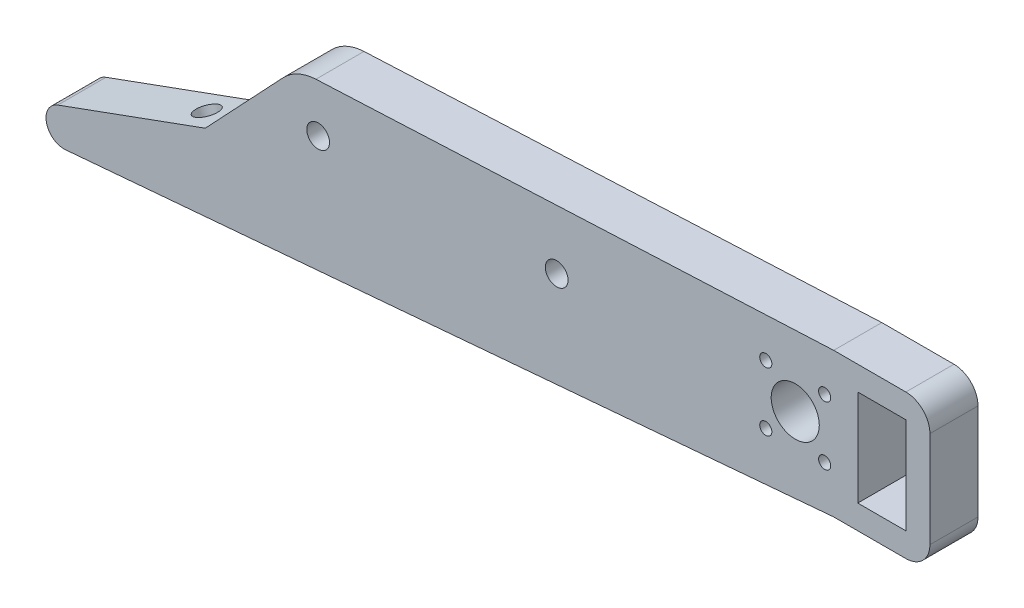
SolidWorks part; units mm, degrees
material "PE High Density"
ref_plane "Front Plane" through (0, 0, 0) normal (0, 0, 1) x (1, 0, 0)
ref_plane "Top Plane" through (0, 0, 0) normal (0, 1, 0) x (1, 0, 0)
ref_plane "Right Plane" through (0, 0, 0) normal (1, 0, 0) x (0, 0, -1)
sketch "Sketch1" plane through (0, 0, 0) normal (0, 0, 1) x (1, 0, 0)
  line L0 (27.6069, 3.8891) -> (35.3851, -3.8891) construction
  line L1 (0, -55) -> (0, 55) construction
  line L2 (27.6069, -3.8891) -> (35.3851, 3.8891) construction
  line L3 (-1001.9207, 0) -> (48998.0793, 0) construction
  line L4 (-969.6313, -19.05) -> (49030.3687, -19.05) construction
  line L5 (36.576, 9.525) -> (49.276, 9.525)
  line L6 (39.751, 6.35) -> (46.101, 6.35)
  line L7 (39.751, 6.35) -> (39.751, -6.35)
  line L8 (39.751, -6.35) -> (46.101, -6.35)
  line L9 (46.101, 6.35) -> (46.101, -6.35)
  line L10 (39.751, 6.35) -> (46.101, -6.35) construction
  line L11 (39.751, -6.35) -> (46.101, 6.35) construction
  line L13 (36.576, -9.525) -> (49.276, -9.525)
  line L14 (36.576, 0) -> (36.576, -9.525) construction
  line L15 (49.276, 9.525) -> (49.276, -9.525)
  line L21 (36.576, 9.525) -> (36.576, 0) construction
  line L22 (36.576, 9.525) -> (36.576, -9.525) construction
  line L23 (-46.398, -6.562) -> (-80.7085, -19.05) construction
  line L24 (49.276, 9.525) -> (49.276, -9.525) construction
  line L25 (36.576, 9.525) -> (-31.7912, 6.3431)
  line L26 (-36.1188, 4.3534) -> (-46.398, -6.562)
  line L27 (-46.398, -6.562) -> (-65.8615, -13.6461)
  line L28 (-64.8428, -18.2563) -> (36.576, -9.525)
  circle A0 centre (31.496, 0) radius 3.175
  circle A1 centre (27.6069, 3.8891) radius 0.8
  circle A2 centre (35.3851, -3.8891) radius 0.8
  circle A4 centre (-31.496, 0) radius 1.5
  circle A5 centre (35.3851, 3.8891) radius 0.8
  circle A6 centre (27.6069, -3.8891) radius 0.8
  circle A7 centre (31.496, 0) radius 19.05 construction
  circle A8 centre (-31.496, 0) radius 19.05 construction
  arc A16 (-31.7912, 6.3431) -> (-36.1188, 4.3534) centre (-31.496, 0) ccw
  circle A17 centre (-29.9085, 22.225) radius 38.1 construction
  arc A18 (-65.8615, -13.6461) -> (-64.8428, -18.2563) centre (-65.0471, -15.8838) ccw
  arc A19 (-37.846, 0) -> (-25.146, 0) centre (-31.496, 0) ccw construction
  arc A21 (-25.146, 0) -> (-31.7912, 6.3431) centre (-31.496, 0) ccw construction
  arc A22 (-36.1188, 4.3534) -> (-37.846, 0) centre (-31.496, 0) ccw construction
  circle A23 centre (0, 0) radius 1.5
  point P6 (31.496, 0)
  point P17 (31.496, 0)
  point P33 (42.926, 0)
  point P51 (-29.9085, -15.875)
  point P52 (-68.0085, 22.225)
  dimension "D1" = 6.35
  dimension "D3" = 62.992
  dimension "D4" = 1.6
  dimension "D7" = 38.1
  dimension "D10" = 12.7
  dimension "D11" = 36.5125
  dimension "D16" = 1.5875
  dimension "D18" = 76.2
  dimension "D6" = 3
  dimension "D9" = 12.7
  dimension "D19" = 4.7625
  dimension "D2" = 11
  dimension "D5" = 45
  dimension "D8" = 20
  dimension "D12" = 6.35
  dimension "D13" = 12.7
  dimension "D15" = 11.43
  dimension "D17" = 3.175
  dimension "D20" = 1.5875
  dimension "D14" = 3.175
extrude "Boss-Extrude1" add sketch "Sketch1" along normal mid plane 6.35 contours L27 A18 L28 L13 L15 L5 L25 A16 L26 A4 A2 A1 A0 L6 L9 L8 L7 A5 A6
fillet "Fillet1" radius 3.175 2 edges at (49.276, -9.525, 0) (49.276, 9.525, 0)
sketch "Sketch2" plane through (-3.3185, 9.1176, 0) normal (-0.342, 0.9397, 0) x (0.9397, 0.342, 0)
  line L1 (-49.0192, 0) -> (-45.8442, 0) construction
  line L2 (-45.8442, -3.175) -> (-45.8442, 3.175) construction
  circle A0 centre (-49.0192, 0) radius 1.5
  dimension "D2" = 3.175
extrude "Cut-Extrude1" cut sketch "Sketch2" against normal blind 6
